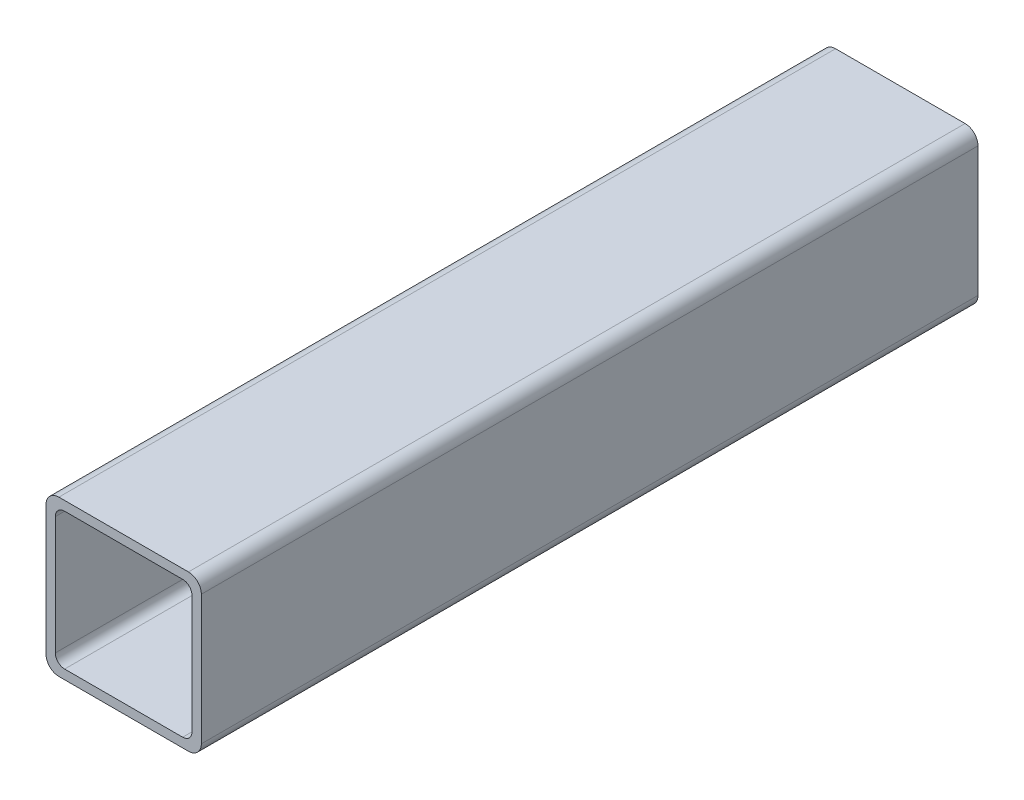
SolidWorks part; units mm, degrees
material "6061 Alloy"
ref_plane "Front Plane" through (0, 0, 0) normal (0, 0, 1) x (1, 0, 0)
ref_plane "Top Plane" through (0, 0, 0) normal (0, 1, 0) x (1, 0, 0)
ref_plane "Right Plane" through (0, 0, 0) normal (1, 0, 0) x (0, 0, -1)
ref_plane "Plane1" through (0, 0, -3683) normal (0, 0, -1) x (-1, 0, 0)
sketch "Sketch1" plane through (0, 0, -3683) normal (0, 0, -1) x (-1, 0, 0)
  line L0 (11.176, 9.652) -> (11.176, -9.652)
  line L1 (9.652, -11.176) -> (-9.652, -11.176)
  line L2 (-11.176, -9.652) -> (-11.176, 9.652)
  line L3 (-9.652, 11.176) -> (9.652, 11.176)
  line L4 (12.7, -10.5918) -> (12.7, 10.5918)
  line L5 (10.5918, 12.7) -> (-10.5918, 12.7)
  line L6 (-12.7, 10.5918) -> (-12.7, -10.5918)
  line L7 (-10.5918, -12.7) -> (10.5918, -12.7)
  arc A0 (11.176, -9.652) -> (9.652, -11.176) centre (9.652, -9.652) cw
  arc A1 (-9.652, -11.176) -> (-11.176, -9.652) centre (-9.652, -9.652) cw
  arc A2 (-11.176, 9.652) -> (-9.652, 11.176) centre (-9.652, 9.652) cw
  arc A3 (9.652, 11.176) -> (11.176, 9.652) centre (9.652, 9.652) cw
  arc A4 (12.7, 10.5918) -> (10.5918, 12.7) centre (10.5918, 10.5918) ccw
  arc A5 (-10.5918, 12.7) -> (-12.7, 10.5918) centre (-10.5918, 10.5918) ccw
  arc A6 (-12.7, -10.5918) -> (-10.5918, -12.7) centre (-10.5918, -10.5918) ccw
  arc A7 (10.5918, -12.7) -> (12.7, -10.5918) centre (10.5918, -10.5918) ccw
extrude "Boss-Extrude1" add sketch "Sketch1" against normal blind 127
